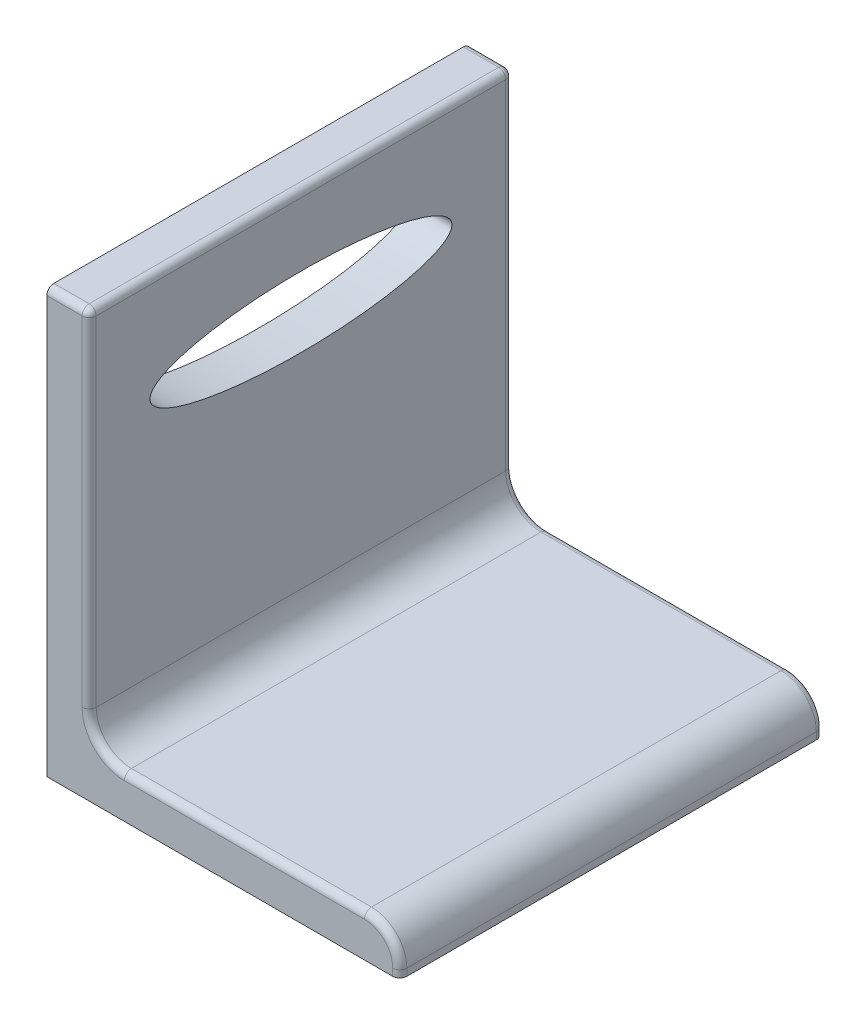
SolidWorks part; units mm, degrees
ref_plane "Plan de face" through (0, 0, 0) normal (0, 0, 1) x (1, 0, 0)
ref_plane "Plan de dessus" through (0, 0, 0) normal (0, 1, 0) x (1, 0, 0)
ref_plane "Plan de droite" through (0, 0, 0) normal (1, 0, 0) x (0, 0, -1)
sketch "Esquisse1" plane through (0, 0, 0) normal (0, 0, 1) x (1, 0, 0)
  line L1 (0, 0) -> (100, 0)
  line L2 (0, 0) -> (0, 12)
  line L3 (0, 12) -> (100, 12)
  line L4 (100, 0) -> (100, 12)
  line L5 (0, 12) -> (12, 12)
  line L6 (0, 12) -> (0, 120)
  line L7 (0, 120) -> (12, 120)
  line L8 (12, 12) -> (12, 120)
  dimension "D1" = 100
  dimension "D2" = 12
  dimension "D3" = 120
  dimension "D4" = 12
extrude "Boss.-Extru.1" add sketch "Esquisse1" against normal blind 120 contours L3 L8 L7 L6 | L1 L4 L3 L2
sketch "Esquisse2" plane through (0, 0, 0) normal (-1, 0, 0) x (0, 0, 1)
  line L0 (-120, 120) -> (0, 120) construction
  ellipse E0 centre (-60, 90) end of major axis (-17.2284, 90) minor radius 10
  dimension "D1" = 60
  dimension "D2" = 30
extrude "Enlèv. mat.-Extru.1" cut sketch "Esquisse2" against normal blind 12 contours E0
fillet "Congé1" radius 10 1 edges at (100, 12, -60)
fillet "Congé2" radius 10 1 edges at (12, 12, -60)
fillet "Congé3" radius 2 5 edges at (100, 1, 0) (12, 71, 0) (14.9289, 14.9289, 0) (56, 12, 0) (97.0711, 9.0711, 0)
fillet "Congé4" radius 2 5 edges at (12, 71, -120) (14.9289, 14.9289, -120) (56, 12, -120) (100, 1, -120) (97.0711, 9.0711, -120)
fillet "Congé5" radius 2 5 edges at (5, 120, -120) (11.4142, 120, -119.4142) (12, 120, -60) (11.4142, 120, -0.5858) (5, 120, 0)
